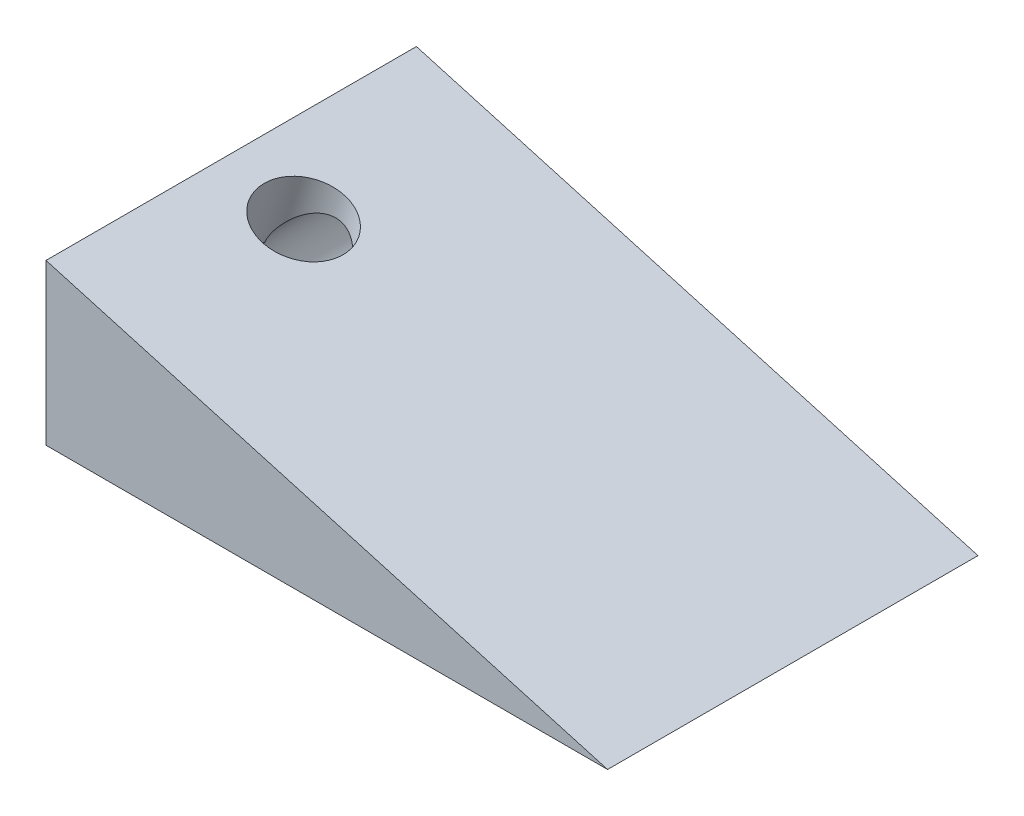
SolidWorks part; units mm, degrees
ref_plane "Front Plane" through (0, 0, 0) normal (0, 0, 1) x (1, 0, 0)
ref_plane "Top Plane" through (0, 0, 0) normal (0, 1, 0) x (1, 0, 0)
ref_plane "Right Plane" through (0, 0, 0) normal (1, 0, 0) x (0, 0, -1)
sketch "Sketch1" plane through (0, 0, 0) normal (0, 0, 1) x (1, 0, 0)
  line L0 (-44.7801, 0) -> (61.3413, 0)
  line L1 (61.3413, 0) -> (-44.7801, 30.2543)
  line L2 (-44.7801, 30.2543) -> (-44.7801, 0)
extrude "Boss-Extrude1" add sketch "Sketch1" along normal blind 70
sketch "Sketch4" plane through (4.6109, 16.1734, 0) normal (0.2742, 0.9617, 0) x (0.9617, -0.2742, 0)
  line L0 (-51.3589, 0) -> (-22.9144, -70)
  line L1 (58.9908, -70) -> (-51.3589, -70) construction
  line L2 (-22.9144, 0) -> (-51.3589, -70)
  line L4 (58.9908, 0) -> (-51.3589, 0) construction
  circle A0 centre (-37.1366, -35) radius 7.7473
extrude "Cut-Extrude1" cut sketch "Sketch4" against normal blind 13 contours A0
sketch "Sketch7" plane through (0, 0, 0) normal (0, 0, -1) x (-1, 0, 0)
  circle A0 centre (33.2042, 13.1412) radius 8.7157
extrude "Cut-Extrude2" cut sketch "Sketch7" against normal blind 40
